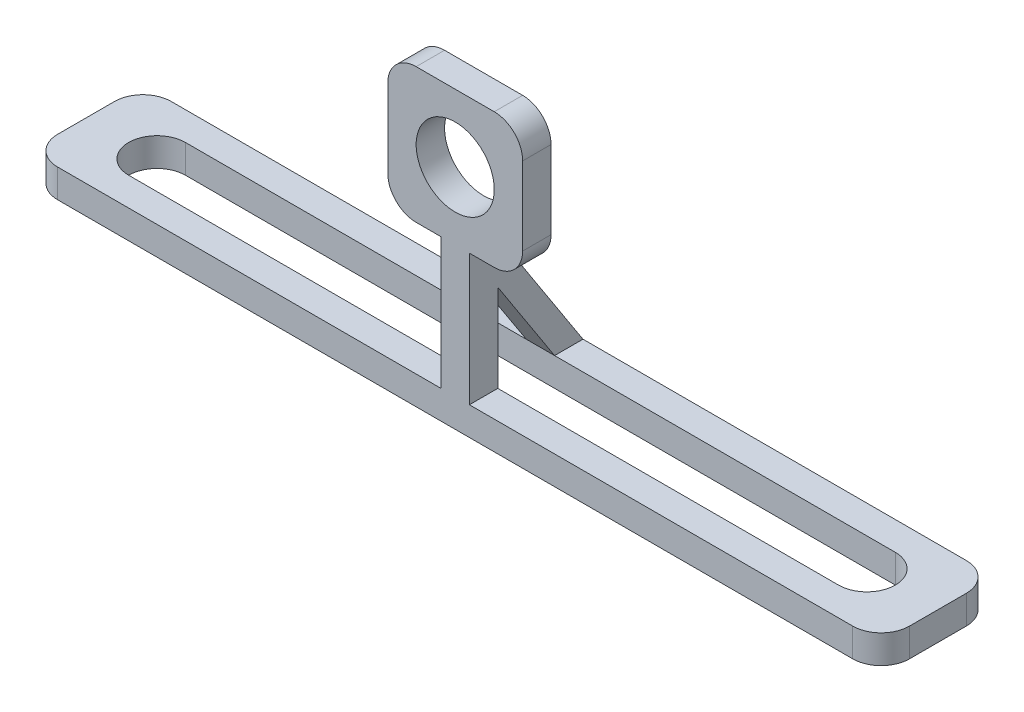
SolidWorks part; units mm, degrees
ref_plane "Front Plane" through (0, 0, 0) normal (0, 0, 1) x (1, 0, 0)
ref_plane "Top Plane" through (0, 0, 0) normal (0, 1, 0) x (1, 0, 0)
ref_plane "Right Plane" through (0, 0, 0) normal (1, 0, 0) x (0, 0, -1)
sketch "Sketch1" plane through (0, 0, 0) normal (0, 1, 0) x (1, 0, 0)
  line L0 (0, 0) -> (30, 0)
  line L1 (30, 0) -> (30, 8)
  line L2 (30, 8) -> (-30, 8)
  line L3 (-30, 8) -> (-30, 0)
  line L4 (-30, 0) -> (0, 0)
  line L5 (-30, 4) -> (-25, 4)
  line L6 (30, 4) -> (25, 4)
  line L7 (-25, 4) -> (25, 4) construction
  line L8 (-25, 6) -> (25, 6)
  line L9 (-25, 2) -> (25, 2)
  arc A0 (-25, 6) -> (-25, 2) centre (-25, 4) ccw
  arc A1 (25, 2) -> (25, 6) centre (25, 4) ccw
  point P10 (0, 4)
  dimension "D6" = 2
  dimension "D1" = 60
  dimension "D2" = 8
  dimension "D3" = 30
  dimension "D4" = 5
  dimension "D5" = 5
extrude "Boss-Extrude1" add sketch "Sketch1" along normal blind 20.75 contours A1 L9 A0 L5 L3 L4 L0 L1 L6 | A1 L6 L1 L2 L3 L5 A0 L8
sketch "Sketch2" plane through (0, 0, 0) normal (0, 0, 1) x (1, 0, 0)
  line L0 (-30, 0) -> (-30, 2)
  line L1 (-30, 20.75) -> (-30, 0) construction
  line L2 (-30, 2) -> (-4.75, 2)
  line L3 (-4.75, 2) -> (-4.75, 20.75)
  line L4 (-30, 20.75) -> (30, 20.75) construction
  line L5 (-4.75, 20.75) -> (-30, 20.75)
  line L6 (-30, 20.75) -> (-30, 2)
  line L7 (30, 0) -> (30, 2)
  line L8 (30, 20.75) -> (30, 0) construction
  line L9 (30, 2) -> (4.75, 2)
  line L10 (4.75, 2) -> (4.75, 20.75)
  line L11 (4.75, 20.75) -> (30, 20.75)
  line L12 (30, 20.75) -> (30, 2)
  line L13 (0, 20.75) -> (0, 18.75)
  line L14 (0, 18.75) -> (0, 16)
  line L15 (0, 13.25) -> (0, 11.25)
  line L16 (0, 11.25) -> (-1, 11.25)
  line L17 (-1, 11.25) -> (-1, 2)
  line L18 (-1, 2) -> (-4.75, 2)
  line L19 (0, 11.25) -> (1, 11.25)
  line L20 (1, 11.25) -> (1, 2)
  line L21 (1, 2) -> (4.75, 2)
  line L22 (-1, 11.25) -> (-4.75, 11.25)
  line L23 (1, 11.25) -> (4.75, 11.25)
  circle A0 centre (0, 16) radius 2.75
  dimension "D3" = 5.5
  dimension "D1" = 2
  dimension "D2" = 2.75
  dimension "D4" = 4.75
  dimension "D5" = 4.75
  dimension "D6" = 2
  dimension "D7" = 2
  dimension "D8" = 1
  dimension "D9" = 1
extrude "Cut-Extrude1" cut sketch "Sketch2" against normal blind 20.75
sketch "Sketch3" plane through (4.75, 0, 0) normal (1, 0, 0) x (0, 0, -1)
  line L0 (6, 20.75) -> (8, 20.75)
  line L1 (8, 20.75) -> (8, 2)
  line L2 (8, 2) -> (6, 2)
  line L3 (6, 2) -> (6, 20.75)
extrude "Cut-Extrude2" cut sketch "Sketch3" against normal blind 20.75
fillet "Fillet1" radius 2 8 edges at (-4.75, 11.25, -1) (4.75, 11.25, -1) (-4.75, 20.75, -1) (4.75, 20.75, -1) (-30, 1, -8) (30, 1, -8) (30, 1, 0) (-30, 1, 0)
sketch "Sketch5" plane through (1, 0, 0) normal (1, 0, 0) x (0, 0, -1)
  line L0 (2, 11.25) -> (8, 2)
  line L1 (8, 2) -> (6, 2)
  line L2 (6, 2) -> (2, 8.1667)
  line L3 (2, 2) -> (2, 11.25) construction
  line L4 (2, 11.25) -> (2, 8.1667)
extrude "Boss-Extrude2" add sketch "Sketch5" against normal blind 2
